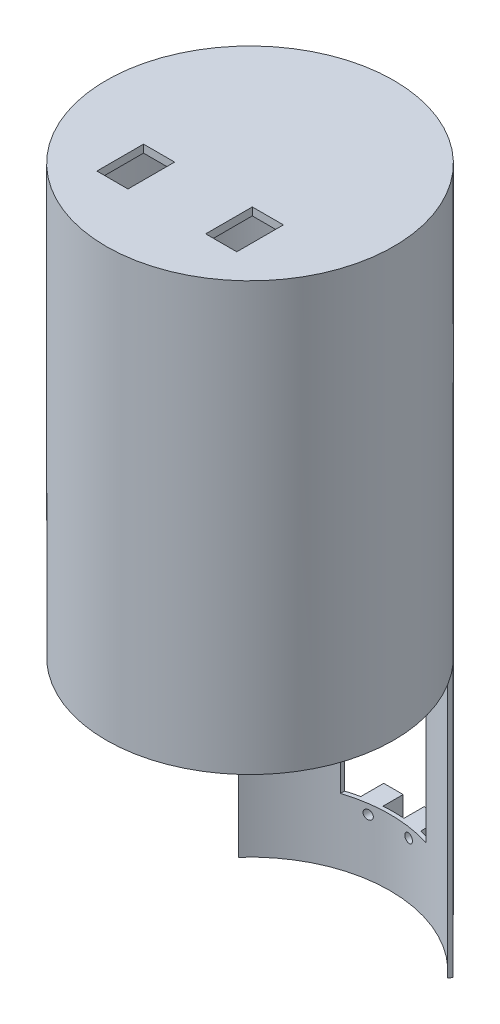
SolidWorks part; units mm, degrees
ref_plane "前基準面" through (0, 0, 0) normal (0, 0, 1) x (1, 0, 0)
ref_plane "上基準面" through (0, 0, 0) normal (0, 1, 0) x (1, 0, 0)
ref_plane "右基準面" through (0, 0, 0) normal (1, 0, 0) x (0, 0, -1)
sketch "草圖1" plane through (0, 0, 0) normal (0, 1, 0) x (1, 0, 0)
  circle A0 centre (0, 0) radius 37
  circle A1 centre (0, 0) radius 36
  dimension "D1" = 74
  dimension "D2" = 72
extrude "填料-伸長1" add sketch "草圖1" along normal blind 110 and the other way blind 70 contours A0
sketch "草圖2" plane through (0, 0, 0) normal (0, 1, 0) x (1, 0, 0)
  line L0 (0, 0) -> (0, 31.9988) construction
  circle A0 centre (0, 0) radius 36
  dimension "D1" = 72
extrude "除料-伸長1" cut sketch "草圖2" along normal blind 108 and the other way blind 70
sketch "草圖6" plane through (0, 0, 0) normal (0, 1, 0) x (1, 0, 0)
  line L0 (-36, 0) -> (26.3008, 0)
  line L1 (0, 0) -> (0, 27.8442) construction
  line L3 (26.3008, 0) -> (36, 0)
  line L5 (-27.5097, 24.743) -> (-26.89, 23.9359)
  line L6 (27.5097, 24.743) -> (26.89, 23.9359)
  arc A0 (-37, 0) -> (37, 0) centre (0, 0) ccw
  circle A1 centre (0, 0) radius 37 construction
  circle A3 centre (0, 0) radius 36 construction
  arc A6 (-37, 0) -> (-27.5097, 24.743) centre (0, 0) cw
  arc A9 (-36, 0) -> (-26.89, 23.9359) centre (0, 0) cw
  circle A10 centre (0, 0) radius 36 construction
  arc A11 (37, 0) -> (27.5097, 24.743) centre (0, 0) ccw
  arc A12 (36, 0) -> (26.89, 23.9359) centre (0, 0) ccw
extrude "除料-伸長6" cut sketch "草圖6" against normal blind 70
ref_plane "平面3" through (0, -10, 0) normal (0, 1, 0) x (1, 0, 0)
sketch "草圖7" plane through (0, -10, 0) normal (0, 1, 0) x (1, 0, 0)
  line L0 (0, 0) -> (0, 28.0951) construction
  line L1 (11, 17.9106) -> (-11, 17.9106)
  line L2 (-11, 17.9106) -> (-11, 37.9106)
  line L3 (-11, 37.9106) -> (11, 37.9106)
  line L4 (11, 17.9106) -> (11, 37.9106)
  point P8 (0, 37.9106)
  point P9 (0, 17.9106)
  dimension "D1" = 11
  dimension "D2" = 20
extrude "除料-伸長7" cut sketch "草圖7" against normal blind 43
sketch "草圖8" plane through (0, 0, 0) normal (0, 1, 0) x (1, 0, 0)
  line L0 (0, 37) -> (0, -37) construction
  line L1 (14, 20.8205) -> (-14, 20.8205)
  line L2 (-14, 20.8205) -> (-14, -20.1795)
  line L3 (-14, -20.1795) -> (14, -20.1795)
  line L4 (14, 20.8205) -> (14, -20.1795)
  circle A1 centre (0, 0) radius 37 construction
  point P11 (0, -20.1795)
  point P12 (0, 20.8205)
  dimension "D1" = 28
  dimension "D2" = 41
sketch "草圖10" plane through (0, 110, 0) normal (0, 1, 0) x (1, 0, 0)
  line L0 (0, 37) -> (0, -37) construction
  line L1 (-17.9922, -9.3977) -> (-9.9922, -9.3977)
  line L2 (-17.9922, -9.3977) -> (-17.9922, -21.3977)
  line L3 (-17.9922, -21.3977) -> (-9.9922, -21.3977)
  line L4 (-9.9922, -9.3977) -> (-9.9922, -21.3977)
  line L5 (17.9922, -21.3977) -> (9.9922, -21.3977)
  line L6 (9.9922, -9.3977) -> (9.9922, -21.3977)
  line L7 (17.9922, -9.3977) -> (9.9922, -9.3977)
  line L8 (17.9922, -9.3977) -> (17.9922, -21.3977)
  dimension "D1" = 8
  dimension "D2" = 12
extrude "除料-伸長8" cut sketch "草圖10" against normal blind 8.1
sketch "草圖11" plane through (0, 0, 0) normal (0, 0, 1) x (1, 0, 0)
  line L0 (0, 0) -> (0, -70) construction
  line L1 (-26.89, -70) -> (26.89, -70) construction
  line L2 (-11, -31.5) -> (11, -31.5) construction
  line L3 (-11, -53) -> (-11, -10) construction
  line L4 (11, -10) -> (11, -53) construction
  line L5 (40.7, -10) -> (-40.7, -10) construction
  line L6 (-7.7, -10) -> (-2.7, -10)
  line L7 (-7.7, -10) -> (-7.7, -5)
  line L8 (-7.7, -5) -> (-2.7, -5)
  line L9 (-2.7, -10) -> (-2.7, -5)
  line L10 (-7.7, -7.5) -> (-2.7, -7.5) construction
  line L11 (-2.7, -7.5) -> (-5.2, -5) construction
  line L12 (-5.2, -5) -> (-5.2, -10) construction
  circle A0 centre (-5.2, -7.5) radius 1.15
  dimension "D4" = 2.3
  dimension "D1" = 3.3
  dimension "D2" = 5
  dimension "D3" = 5
ref_plane "平面4" through (0, 0, -37) normal (0, 0, 1) x (1, 0, 0)
sketch "草圖12" plane through (0, 0, -37) normal (0, 0, 1) x (1, 0, 0)
  line L0 (0, 0) -> (0, -70) construction
  line L1 (-7.7, -5) -> (-2.7, -5)
  line L2 (-7.7, -5) -> (-7.7, -10)
  line L3 (-7.7, -10) -> (-2.7, -10)
  line L4 (-2.7, -5) -> (-2.7, -10)
  line L5 (-11, -31.5) -> (11, -31.5) construction
  line L6 (7.7, -10) -> (2.7, -10)
  line L7 (7.7, -5) -> (7.7, -10)
  line L8 (7.7, -5) -> (2.7, -5)
  line L9 (2.7, -5) -> (2.7, -10)
  line L10 (7.7, -58) -> (7.7, -53)
  line L11 (7.7, -53) -> (2.7, -53)
  line L12 (2.7, -58) -> (2.7, -53)
  line L13 (7.7, -58) -> (2.7, -58)
  line L14 (-7.7, -53) -> (-2.7, -53)
  line L15 (-7.7, -58) -> (-7.7, -53)
  line L16 (-7.7, -58) -> (-2.7, -58)
  line L17 (-2.7, -58) -> (-2.7, -53)
  circle A0 centre (-5.2, -7.5) radius 1.15
  circle A1 centre (5.2, -7.5) radius 1.15
  circle A2 centre (5.2, -55.5) radius 1.15
  circle A3 centre (-5.2, -55.5) radius 1.15
  dimension "D1" = 2.3
extrude "填料-伸長3" add sketch "草圖12" against normal blind 5.1 and the other way blind 1
sketch "草圖13" plane through (0, 0, -37) normal (0, 0, 1) x (1, 0, 0)
  line L0 (0, 0) -> (0, -53.5237) construction
  line L1 (0, 0) -> (0, -70) construction
  line L2 (11, -31.5) -> (-11, -31.5) construction
  circle A0 centre (5.2, -7.5) radius 1.15
  circle A1 centre (-5.2, -7.5) radius 1.15
  circle A2 centre (-5.2, -55.5) radius 1.15
  circle A3 centre (5.2, -55.5) radius 1.15
extrude "除料-伸長9" cut sketch "草圖13" along normal blind 18.4
